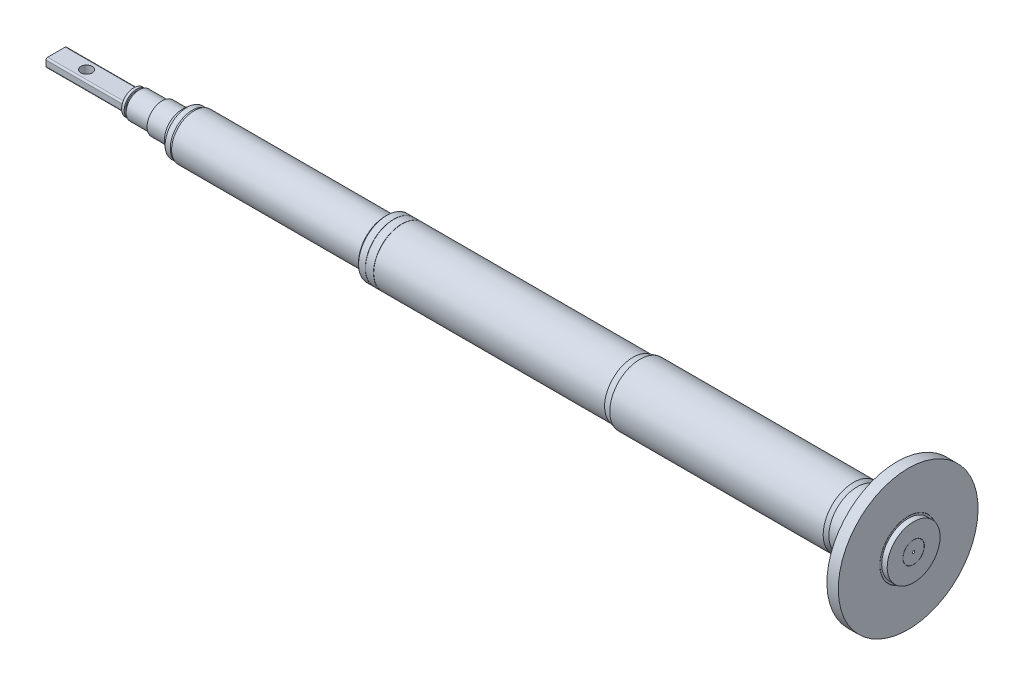
SolidWorks part; units mm, degrees
other "FEI Body"
other "FEI O-Ring"
other "Nion PTFE Bumper"
other "Nion O-Ring"
other "Nion Retaining Ring"
other "Nion Back Plate"
other "Nion Sleeve" parameters "D6"=4.9293, "D1"=6, "D2"=31.0799, "D3"=398.2809, "D4"=4, "D5"=0.2861, "D7"=31.0799, "D8"=0.5151, "D9"=0.4648, "D10"=84.2763, "D11"=31.0799, "D12"=149.1697, "D13"=222.1348, "D14"=31.0799, "D15"=211.4611, "D16"=58.412, "D17"=56.5, "D18"=7.7471, "D19"=0.8678, "D20"=0.9951, "D21"=0.7684, "D23"=1.45, "D24"=2.1166, "D26"=10.9151, "D27"=6.8987, "D29"=3, "D30"=90, "D31"=8.9564, "D32"=1.4786, "D33"=31.0799, "D34"=398.2809, "D35"=0.675, "D36"=0.7893, "D22"=0.05, "D25"=0.05, "D28"=0.05
ref_plane "Front Plane" through (0, 0, 0) normal (0, 0, 1) x (1, 0, 0)
ref_plane "Top Plane" through (0, 0, 0) normal (0, 1, 0) x (1, 0, 0)
ref_plane "Right Plane" through (0, 0, 0) normal (1, 0, 0) x (0, 0, -1)
sketch "Sketch1" plane through (0, 0, 0) normal (0, 0, 1) x (1, 0, 0)
  line L0 (103.225, 0) -> (-103.225, 0) construction
  line L4 (-101.775, 3.5) -> (0.225, 3.5)
  line L5 (0.225, 3.5) -> (2.725, 6)
  line L6 (2.725, 6) -> (5.625, 6)
  line L7 (5.625, 6) -> (5.675, 4.5)
  line L8 (5.675, 4.5) -> (8.175, 4.5)
  line L9 (8.175, 4.5) -> (8.225, 6)
  line L10 (8.225, 6) -> (87.725, 6)
  line L11 (87.725, 6) -> (89.225, 7)
  line L12 (89.225, 7) -> (103.225, 7)
  line L13 (103.225, 7) -> (103.225, 0) construction
  line L14 (6.925, 4.5) -> (6.925, 6) construction
  line L15 (5.625, 6) -> (8.225, 6) construction
  line L16 (5.7249, 6.0033) -> (5.7717, 4.6)
  line L17 (5.7717, 4.6) -> (8.0783, 4.6)
  line L18 (8.0783, 4.6) -> (8.1251, 6.0033)
  line L19 (5.7249, 6.0033) -> (8.1251, 6.0033)
  line L20 (-101.775, 3.5) -> (-101.775, 2.85)
  line L21 (-101.775, 2.85) -> (103.225, 2.85)
  line L22 (103.225, 2.85) -> (103.225, 7)
  line L24 (-102.525, 2.8) -> (-102.525, 3.25)
  line L25 (-102.525, 3.25) -> (-103.225, 3.25)
  line L26 (-103.225, 3.25) -> (-103.225, 0.3)
  line L27 (-103.225, 0.3) -> (103.225, 0.3)
  line L28 (103.225, 0.3) -> (103.225, 2.8)
  line L29 (103.225, 2.8) -> (-102.525, 2.8)
  point P3 (6.925, 6)
  point P18 (0, 0)
  dimension "D2" = 3.5
  dimension "D3" = 6
  dimension "D4" = 1.5
  dimension "D5" = 1
  dimension "D6" = 14
  dimension "D7" = 1.5
  dimension "D8" = 95
  dimension "D9" = 100.5
  dimension "D10" = 2.5
  dimension "D11" = 102
  dimension "D12" = 0.75
  dimension "D13" = 2.5
  dimension "D14" = 2.6
  dimension "D16" = 0.3
  dimension "D17" = 3.25
  dimension "D18" = 0.05
  dimension "D19" = 0.7
  dimension "D20" = 2.5
  dimension "D15" = 0.1
revolve "FEI Body Revolve" add sketch "Sketch1" angle 360 about L0
sketch "Sketch42" plane through (-103.225, 0, 0) normal (-1, 0, 0) x (0, 0, 1)
  line L0 (-2.8866, 0) -> (2.8866, 0) construction
  line L1 (0, 1.15) -> (0, -1.15) construction
  line L2 (-2.3208, 1.15) -> (2.3208, 1.15)
  line L4 (2.75, 0.7208) -> (2.75, -0.7208)
  line L6 (2.3208, -1.15) -> (-2.3208, -1.15)
  line L7 (2.75, 1.2672) -> (2.75, -1.2672) construction
  line L8 (-2.75, 0.7208) -> (-2.75, -0.7208)
  arc A0 (2.3208, 1.15) -> (2.75, 0.7208) centre (2.3208, 0.7208) cw
  arc A1 (2.75, -0.7208) -> (2.3208, -1.15) centre (2.3208, -0.7208) cw
  arc A2 (-2.75, -0.7208) -> (-2.3208, -1.15) centre (-2.3208, -0.7208) ccw
  arc A3 (-2.3208, 1.15) -> (-2.75, 0.7208) centre (-2.3208, 0.7208) ccw
  circle A4 centre (0, 0) radius 0.3 construction
  circle A5 centre (0, 0) radius 0.3
  point P5 (0, 0)
  point P6 (0, 0)
  point P15 (2.75, 0)
  circle M16 centre (0, 0) radius 0.3
  dimension "D1" = 2.75
  dimension "D2" = 2.3
extrude "Tip - Front Profile Extrude" add sketch "Sketch42" along normal blind 20.5 contours M16 | L2 A3 L8 A2 L6 A1 L4 A0 M16
sketch "Sketch43" plane through (0, 1.15, 0) normal (0, 1, 0) x (1, 0, 0)
  line L0 (0, 0) -> (-123.725, 0) construction
  line L1 (-123.725, 2.3208) -> (-123.725, -2.3208) construction
  line L5 (-103.225, 2.3208) -> (-103.225, -2.3208) construction
  circle A0 centre (-115.725, 0) radius 1.5
  point P18 (0, 0)
  dimension "D2" = 3
  dimension "D3" = 8
extrude "Tip - Top Profile Cut" cut sketch "Sketch43" against normal through all
sketch "Sketch2" plane through (0, 0, 0) normal (0, 0, 1) x (1, 0, 0)
  line L2 (103.225, 7) -> (89.225, 7) construction
  line L3 (89.225, 7) -> (87.725, 6) construction
  line L4 (87.725, 6) -> (8.225, 6) construction
  line L5 (5.625, 6) -> (2.725, 6) construction
  line L6 (2.725, 6) -> (0.225, 3.5) construction
  line L7 (0.225, 3.5) -> (-101.775, 3.5) construction
  line L8 (103.225, 7) -> (89.225, 7) construction
  line L9 (89.225, 7) -> (87.725, 6)
  line L10 (87.725, 6) -> (8.225, 6)
  line L11 (5.625, 6) -> (2.725, 6)
  line L12 (2.725, 6) -> (0.225, 3.5)
  line L13 (0.225, 3.5) -> (-101.775, 3.5) construction
  line L14 (-115.725, 15) -> (-115.725, -15) construction
  line L15 (5.625, 6) -> (8.225, 6)
  line L16 (-95.725, 3.5) -> (0.225, 3.5)
  line L17 (89.225, 7) -> (101.775, 7)
  line L18 (101.775, 7) -> (101.775, 7.45)
  line L19 (101.775, 7.45) -> (100.725, 7.45)
  line L20 (100.725, 7.45) -> (100.725, 10.45)
  line L21 (100.725, 10.45) -> (98.775, 10.45)
  line L22 (98.775, 10.45) -> (98.775, 8)
  line L23 (98.775, 8) -> (97.475, 8)
  line L24 (97.475, 8) -> (96.475, 7.5)
  line L25 (96.475, 7.5) -> (88.275, 7.5)
  line L26 (88.275, 7.5) -> (87.275, 8)
  line L27 (87.275, 8) -> (30.775, 8)
  line L28 (30.775, 8) -> (28.909, 7.5)
  line L29 (28.909, 7.5) -> (-32.225, 7.5)
  line L30 (-32.225, 7.5) -> (-32.225, 6)
  line L31 (-32.225, 6) -> (-87.225, 6)
  line L32 (-87.225, 6) -> (-87.7745, 5.8)
  line L33 (-87.7745, 5.8) -> (-89.1442, 5.8)
  line L34 (-90.545, 4.5495) -> (-90.545, 4)
  line L35 (-90.545, 4) -> (-95.725, 4)
  line L36 (-95.725, 4) -> (-95.725, 3.5)
  line L37 (200, 0) -> (-200, 0) construction
  line L38 (-85.225, 15) -> (-85.225, -15) construction
  line L39 (-32.225, 7.5) -> (-36.225, 7.5) construction
  line L40 (-36.225, 7.5) -> (-36.725, 7) construction
  line L41 (-36.725, 7) -> (-36.725, 6) construction
  line L42 (-32.275, 7.5) -> (-32.275, 6.05) construction
  line L43 (-32.275, 6.05) -> (-87.225, 6.05) construction
  line L44 (-32.275, 7.5) -> (-32.275, 6.05)
  line L45 (-32.275, 6.05) -> (-34.3916, 6.05)
  line L46 (-34.3916, 6.05) -> (-34.3916, 7.5)
  line L47 (-34.3916, 7.5) -> (-32.275, 7.5)
  line L48 (-34.4416, 7.5) -> (-36.225, 7.5)
  line L49 (-36.225, 7.5) -> (-36.725, 7)
  line L50 (-36.725, 7) -> (-36.725, 6.8)
  line L51 (-36.725, 6.8) -> (-35.875, 6.8)
  line L52 (-35.875, 6.8) -> (-35.875, 6.05)
  line L53 (-35.875, 6.05) -> (-34.4416, 6.05)
  line L54 (-34.4416, 6.05) -> (-34.4416, 7.5)
  line L55 (-36.725, 6.75) -> (-35.925, 6.75)
  line L56 (-35.925, 6.75) -> (-35.925, 6.05)
  line L57 (-36.725, 6.75) -> (-36.725, 6.05)
  line L58 (-36.725, 6.05) -> (-35.925, 6.05)
  line L59 (87.275, 8) -> (97.475, 8) construction
  line L60 (92.375, 7.5) -> (92.375, 8) construction
  line L61 (101.775, 7.5) -> (100.775, 7.5)
  line L62 (100.775, 7.5) -> (100.775, 10.5)
  line L63 (100.775, 10.5) -> (98.775, 10.5)
  line L64 (98.775, 10.5) -> (98.775, 18.5)
  line L65 (98.775, 18.5) -> (101.775, 18.5)
  line L66 (101.775, 18.5) -> (101.775, 7.5)
  line L67 (-115.725, -1.15) -> (-115.725, 1.15) construction
  arc A1 (-90.545, 4.5495) -> (-89.1442, 5.8) centre (-85.225, 0) cw
  point P33 (0, 0)
  point P40 (-85.225, 0)
  point P64 (-115.725, 0)
  dimension "D6" = 7
  dimension "D2" = 20
  dimension "D3" = 4
  dimension "D4" = 5.18
  dimension "D5" = 20
  dimension "D7" = 30.5
  dimension "D8" = 2
  dimension "D9" = 5.8
  dimension "D10" = 6
  dimension "D11" = 83.5
  dimension "D12" = 146.5
  dimension "D14" = 203
  dimension "D15" = 214.5
  dimension "D16" = 15
  dimension "D17" = 8
  dimension "D18" = 7.5
  dimension "D19" = 4.5
  dimension "D20" = 45
  dimension "D21" = 0.5
  dimension "D23" = 0.05
  dimension "D24" = 2.1166
  dimension "D26" = 10.5
  dimension "D27" = 2.3
  dimension "D13" = 3
  dimension "D29" = 18.5
  dimension "D30" = 8
  dimension "D31" = 11
  dimension "D32" = 2
  dimension "D33" = 30
  dimension "D34" = 400
  dimension "D35" = 0.7
  dimension "D36" = 0.8
revolve "Nion Sleeve Revolve" add sketch "Sketch2" angle 360 about L37
equation "\"D23@Sketch2\"= \"D22@Sketch2\""
